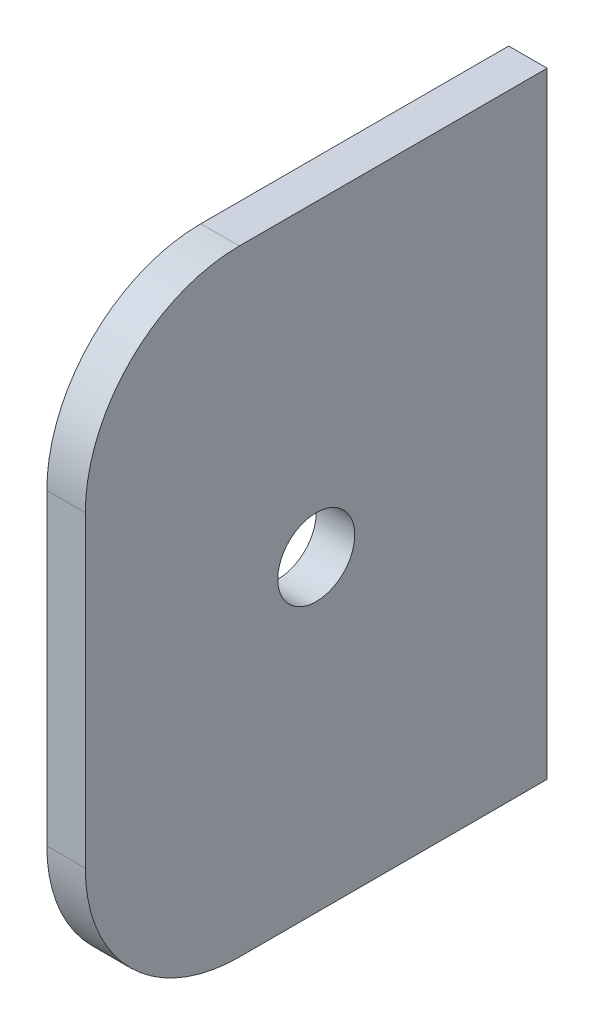
SolidWorks part; units mm, degrees
ref_plane "Front Plane" through (0, 0, 0) normal (0, 0, 1) x (1, 0, 0)
ref_plane "Top Plane" through (0, 0, 0) normal (0, 1, 0) x (1, 0, 0)
ref_plane "Right Plane" through (0, 0, 0) normal (1, 0, 0) x (0, 0, -1)
sketch "Sketch1" plane through (0, 0, 0) normal (0, 0, 1) x (1, 0, 0)
  line L1 (19.05, 1.016) -> (15.875, 1.016)
  line L2 (19.05, 1.016) -> (19.05, -49.784)
  line L3 (19.05, -49.784) -> (15.875, -49.784)
  line L4 (15.875, 1.016) -> (15.875, -49.784)
  dimension "D1" = 50.8
  dimension "D2" = 3.175
extrude "Boss-Extrude1" add sketch "Sketch1" along normal blind 38.1 contours L4 L3 L2 L1
sketch "Sketch3" plane through (15.875, 0, 0) normal (-1, 0, 0) x (0, 0, 1)
  line L0 (38.1, 1.016) -> (38.1, -49.784) construction
  line L1 (38.1, 1.016) -> (0, 1.016) construction
  circle A0 centre (19.05, -24.384) radius 3.175
  point P4 (38.1, -24.384)
  point P5 (38.1, -24.384)
  point P6 (38.1, -24.384)
  point P7 (25.0602, -24.384)
  point P10 (19.05, 1.016)
  dimension "D1" = 6.35
extrude "Cut-Extrude1" cut sketch "Sketch3" against normal blind 38.1
fillet "Fillet1" radius 12.7 2 edges at (17.4625, 1.016, 38.1) (17.4625, -49.784, 38.1)
